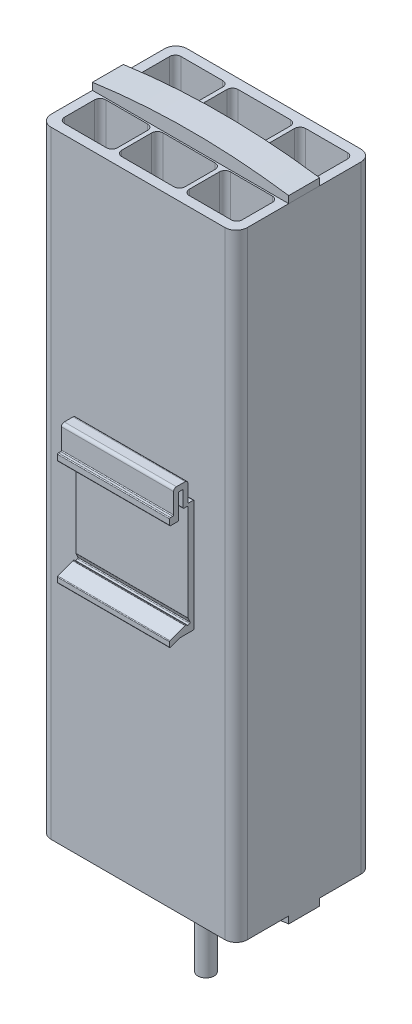
SolidWorks part; units mm, degrees
ref_plane "Спереди" through (0, 0, 0) normal (0, 0, 1) x (1, 0, 0)
ref_plane "Сверху" through (0, 0, 0) normal (0, 1, 0) x (1, 0, 0)
ref_plane "Справа" through (0, 0, 0) normal (1, 0, 0) x (0, 0, -1)
sketch "Эскиз1" plane through (0, 0, 0) normal (0, 0, 1) x (1, 0, 0)
  line L1 (-35, -110) -> (35, -110)
  line L2 (-35, -110) -> (-35, 110)
  line L3 (-35, 110) -> (35, 110)
  line L4 (35, -110) -> (35, 110)
  line L5 (-35, -110) -> (35, 110) construction
  line L6 (-35, 110) -> (35, -110) construction
  point P0 (0, 0)
  dimension "D1" = 70
  dimension "D2" = 220
extrude "Бобышка-Вытянуть1" add sketch "Эскиз1" along normal blind 48.5
sketch "Эскиз2" plane through (0, 110, 0) normal (0, 1, 0) x (1, 0, 0)
  line L0 (0, 0) -> (0, -10.85) construction
  line L1 (-11.3, -3.5) -> (11.3, -3.5)
  line L2 (-11.3, -3.5) -> (-11.3, -18.2)
  line L3 (-11.3, -18.2) -> (11.3, -18.2)
  line L4 (11.3, -3.5) -> (11.3, -18.2)
  line L5 (-11.3, -3.5) -> (11.3, -18.2) construction
  line L6 (-11.3, -18.2) -> (11.3, -3.5) construction
  line L7 (12.8, -3.5) -> (31.7, -3.5)
  line L8 (12.8, -3.5) -> (12.8, -18.2)
  line L9 (12.8, -18.2) -> (31.7, -18.2)
  line L10 (31.7, -3.5) -> (31.7, -18.2)
  line L11 (12.8, -3.5) -> (31.7, -18.2) construction
  line L12 (12.8, -18.2) -> (31.7, -3.5) construction
  line L13 (-31.7, -3.5) -> (-12.8, -3.5)
  line L14 (-31.7, -3.5) -> (-31.7, -18.2)
  line L15 (-31.7, -18.2) -> (-12.8, -18.2)
  line L16 (-12.8, -3.5) -> (-12.8, -18.2)
  line L17 (-31.7, -3.5) -> (-12.8, -18.2) construction
  line L18 (-31.7, -18.2) -> (-12.8, -3.5) construction
  line L19 (35, 0) -> (-35, 0) construction
  line L20 (-35, -24.25) -> (35, -24.25) construction
  line L21 (-35, -48.5) -> (-35, 0) construction
  line L22 (35, -48.5) -> (35, 0) construction
  line L23 (12.8, -30.3) -> (31.7, -30.3)
  line L24 (31.7, -45) -> (31.7, -30.3)
  line L25 (12.8, -45) -> (31.7, -45)
  line L26 (12.8, -45) -> (12.8, -30.3)
  line L27 (-11.3, -30.3) -> (11.3, -30.3)
  line L28 (11.3, -45) -> (11.3, -30.3)
  line L29 (-11.3, -45) -> (11.3, -45)
  line L30 (-11.3, -45) -> (-11.3, -30.3)
  line L31 (-31.7, -30.3) -> (-12.8, -30.3)
  line L32 (-12.8, -45) -> (-12.8, -30.3)
  line L33 (-31.7, -45) -> (-12.8, -45)
  line L34 (-31.7, -45) -> (-31.7, -30.3)
  point P0 (0, -10.85)
  point P5 (22.25, -10.85)
  point P10 (-22.25, -10.85)
  dimension "D1" = 22.6
  dimension "D2" = 18.9
  dimension "D3" = 1.5
  dimension "D4" = 1.5
  dimension "D5" = 3.5
  dimension "D6" = 14.7
extrude "Вырез-Вытянуть1" cut sketch "Эскиз2" against normal up to next
sketch "Эскиз3" plane through (0, 110, 0) normal (0, 1, 0) x (1, 0, 0)
  line L0 (35, -48.5) -> (35, 0) construction
  line L1 (-35, -29.75) -> (35, -29.75)
  line L2 (-35, -29.75) -> (-35, -18.75)
  line L3 (-35, -18.75) -> (35, -18.75)
  line L4 (35, -29.75) -> (35, -18.75)
  line L5 (-35, -29.75) -> (35, -18.75) construction
  line L6 (-35, -18.75) -> (35, -29.75) construction
  line L7 (0, 0) -> (0, -24.25) construction
  line L8 (35, 0) -> (-35, 0) construction
  line L9 (0, -24.25) -> (35, -24.25) construction
  point P0 (0, -24.25)
  point P11 (0, -24.4908)
  point P13 (35, -26.6567)
  point P14 (35, -27.6078)
  point P15 (35, -24.25)
  dimension "D1" = 11
extrude "Бобышка-Вытянуть2" add sketch "Эскиз3" along normal blind 5 separate body
sketch "Эскиз4" plane through (0, 0, 29.75) normal (0, 0, 1) x (1, 0, 0)
  line L0 (-35, 115) -> (-35, 110) construction
  line L1 (35, 115) -> (35, 110) construction
  line L2 (-35, 115) -> (35, 115) construction
  line L3 (-35, 110) -> (35, 110) construction
  line L4 (-35, 112.5) -> (-35, 118.5)
  line L5 (-35, 118.5) -> (35, 118.5)
  line L6 (35, 118.5) -> (35, 112.5)
  arc A0 (-35, 112.5) -> (35, 112.5) centre (0, -131.25) cw
  point P3 (0, 115)
  dimension "D1" = 2.5
  dimension "D2" = 6
extrude "Вырез-Вытянуть4" cut sketch "Эскиз4" against normal up to surface (11 mm away) up to face at (0, 112.5, 18.75)
ref_plane "Плоскость1" through (0, 0, 0) normal (0, 1, 0) x (1, 0, 0)
mirror "Зеркальное отражение2" about plane through (0, 0, 0) normal (0, 1, 0) of "Вырез-Вытянуть4", "Бобышка-Вытянуть2"
ref_plane "Плоскость2" through (0, 0, 24.25) normal (0, 0, -1) x (-1, 0, 0)
sketch "Эскиз5" plane through (0, 0, 24.25) normal (0, 0, -1) x (-1, 0, 0)
  line L7 (-11.5, -124.3774) -> (-17.5, -114.3774)
  line L9 (-11.5, -124.3774) -> (-6.15, -124.3774)
  line L10 (-6.15, -124.3774) -> (-6.15, -127.3774)
  line L11 (-6.15, -127.3774) -> (6.15, -127.3774)
  line L12 (6.15, -124.3774) -> (6.15, -127.3774)
  line L13 (0, 0) -> (0, -127.3774) construction
  line L14 (11.5, -124.3774) -> (6.15, -124.3774)
  line L15 (11.5, -124.3774) -> (17.5, -114.3774)
  arc A0 (-35, -112.5) -> (35, -112.5) centre (0, 131.25) ccw construction
  arc A1 (-17.5, -114.3774) -> (17.5, -114.3774) centre (0, 131.25) ccw
  dimension "D1" = 6.15
  dimension "D2" = 11.5
  dimension "D3" = 17.5
  dimension "D4" = 10
  dimension "D5" = 3
extrude "Бобышка-Вытянуть3" add sketch "Эскиз5" along normal up to surface and the other way up to surface up to face at (0, -111.875, 18.75) other way up to face at (0, -111.875, 29.75)
ref_plane "Плоскость3" through (0, 0, 0) normal (-1, 0, 0) x (0, 0, 1)
sketch "Эскиз11" plane through (0, 0, 0) normal (-1, 0, 0) x (0, 0, 1)
  line L0 (48.8, -19.7) -> (53.4465, -19.7)
  line L1 (53.5502, -19.7185) -> (56.8963, -20.9513)
  line L2 (57.3, -20.6698) -> (57.3, -19.0712)
  line L3 (57.1037, -18.7897) -> (51.7533, -16.8185)
  line L4 (51.6496, -16.8) -> (51.3956, -16.8)
  line L5 (51.1229, -16.975) -> (51.0531, -17.1273)
  line L6 (50.6554, -17.275) -> (50.1099, -17.025)
  line L7 (49.9622, -16.6273) -> (50.6727, -15.0772)
  line L8 (50.7, -14.9522) -> (50.7, 19.3)
  line L9 (51, 19.6) -> (52.1, 19.6)
  line L10 (52.4, 19.9) -> (52.4, 25.3)
  line L11 (52.7, 25.6) -> (53.8, 25.6)
  line L12 (54.1, 25.3) -> (54.1, 16.9)
  line L13 (54.4, 16.6) -> (56.9, 16.6)
  line L14 (57.2, 16.9) -> (57.2, 18.8)
  line L15 (56.9, 19.1) -> (56.1, 19.1)
  line L16 (55.8, 19.4) -> (55.8, 26.6)
  line L17 (54.8, 27.6) -> (51.7, 27.6)
  line L18 (50.7, 26.6) -> (50.7, 20.7)
  line L19 (50.4, 20.4) -> (48.8, 20.4)
  line L20 (48.5, 20.1) -> (48.5, -19.4)
  line L21 (48.5, 110) -> (48.5, -110) construction
  line L22 (48.5, 110) -> (0, 110) construction
  arc A0 (48.8, -19.7) -> (48.5, -19.4) centre (48.8, -19.4) cw
  arc A1 (53.4465, -19.7) -> (53.5502, -19.7185) centre (53.4465, -20) cw
  arc A2 (57.3, -19.0712) -> (57.1037, -18.7897) centre (57, -19.0712) ccw
  arc A3 (56.8963, -20.9513) -> (57.3, -20.6698) centre (57, -20.6698) ccw
  arc A4 (51.7533, -16.8185) -> (51.6496, -16.8) centre (51.6496, -17.1) ccw
  arc A5 (51.3956, -16.8) -> (51.1229, -16.975) centre (51.3956, -17.1) ccw
  arc A6 (50.6727, -15.0772) -> (50.7, -14.9522) centre (50.4, -14.9522) ccw
  arc A7 (50.1099, -17.025) -> (49.9622, -16.6273) centre (50.2349, -16.7523) cw
  arc A8 (51.0531, -17.1273) -> (50.6554, -17.275) centre (50.7804, -17.0023) cw
  arc A9 (54.1, 16.9) -> (54.4, 16.6) centre (54.4, 16.9) ccw
  arc A10 (56.9, 16.6) -> (57.2, 16.9) centre (56.9, 16.9) ccw
  arc A11 (57.2, 18.8) -> (56.9, 19.1) centre (56.9, 18.8) ccw
  arc A12 (56.1, 19.1) -> (55.8, 19.4) centre (56.1, 19.4) cw
  arc A13 (48.8, 20.4) -> (48.5, 20.1) centre (48.8, 20.1) ccw
  arc A14 (50.7, 20.7) -> (50.4, 20.4) centre (50.4, 20.7) cw
  arc A15 (50.7, 19.3) -> (51, 19.6) centre (51, 19.3) cw
  arc A16 (52.1, 19.6) -> (52.4, 19.9) centre (52.1, 19.9) ccw
  arc A17 (52.4, 25.3) -> (52.7, 25.6) centre (52.7, 25.3) cw
  arc A18 (53.8, 25.6) -> (54.1, 25.3) centre (53.8, 25.3) cw
  arc A19 (51.7, 27.6) -> (50.7, 26.6) centre (51.7, 26.6) ccw
  arc A20 (55.8, 26.6) -> (54.8, 27.6) centre (54.8, 26.6) ccw
  point P21 (53.25, 25.6)
  point P22 (53.25, 27.6)
  point P65 (48.5, 97.6)
  dimension "D7" = 0.3
  dimension "D8" = 1
  dimension "D1" = 2.1
  dimension "D2" = 2.2
  dimension "D3" = 47.3
  dimension "D4" = 6.5
  dimension "D5" = 2
  dimension "D6" = 11
  dimension "D9" = 7.2
  dimension "D10" = 12.4
extrude "Бобышка-Вытянуть6" add sketch "Эскиз11" along normal mid plane 40
fillet "Скругление1" radius 4 4 edges at (35, 0, 0) (35, 0, 48.5) (-35, 0, 0) (-35, 0, 48.5)
fillet "Скругление2" radius 2 24 edges at (-12.8, 0, 3.5) (-12.8, 0, 18.2) (-31.7, 0, 18.2) (-31.7, 0, 3.5) (-11.3, 0, 3.5) (-11.3, 0, 18.2) (11.3, 0, 18.2) (11.3, 0, 3.5) (31.7, 0, 18.2) (12.8, 0, 18.2) (12.8, 0, 3.5) (31.7, 0, 3.5) (31.7, 0, 30.3) (12.8, 0, 30.3) (12.8, 0, 45) (31.7, 0, 45) (11.3, 0, 45) (11.3, 0, 30.3) (-11.3, 0, 30.3) (-11.3, 0, 45) (-12.8, 0, 45) (-12.8, 0, 30.3) (-31.7, 0, 30.3) (-31.7, 0, 45)
sketch "Эскиз13" plane through (0, -127.3774, 0) normal (0, -1, 0) x (1, 0, 0)
  line L0 (-35, 29.75) -> (35, 29.75) construction
  line L1 (0, 30.3) -> (0, 24.25) construction
  line L2 (-9.3, 30.3) -> (9.3, 30.3) construction
  line L3 (0, 24.25) -> (6.15, 24.25) construction
  line L4 (6.15, 18.75) -> (6.15, 29.75) construction
  circle A0 centre (0, 24.25) radius 5.5
extrude "Вырез-Вытянуть8" cut sketch "Эскиз13" against normal up to surface (3 mm away) flip side to cut up to face at (-8.825, -124.3774, 24.25)
sketch "Эскиз14" plane through (0, -127.3774, 0) normal (0, -1, 0) x (1, 0, 0)
  circle A0 centre (0, 24.25) radius 2.9
  dimension "D1" = 5.8
extrude "Бобышка-Вытянуть7" add sketch "Эскиз14" along normal blind 20
